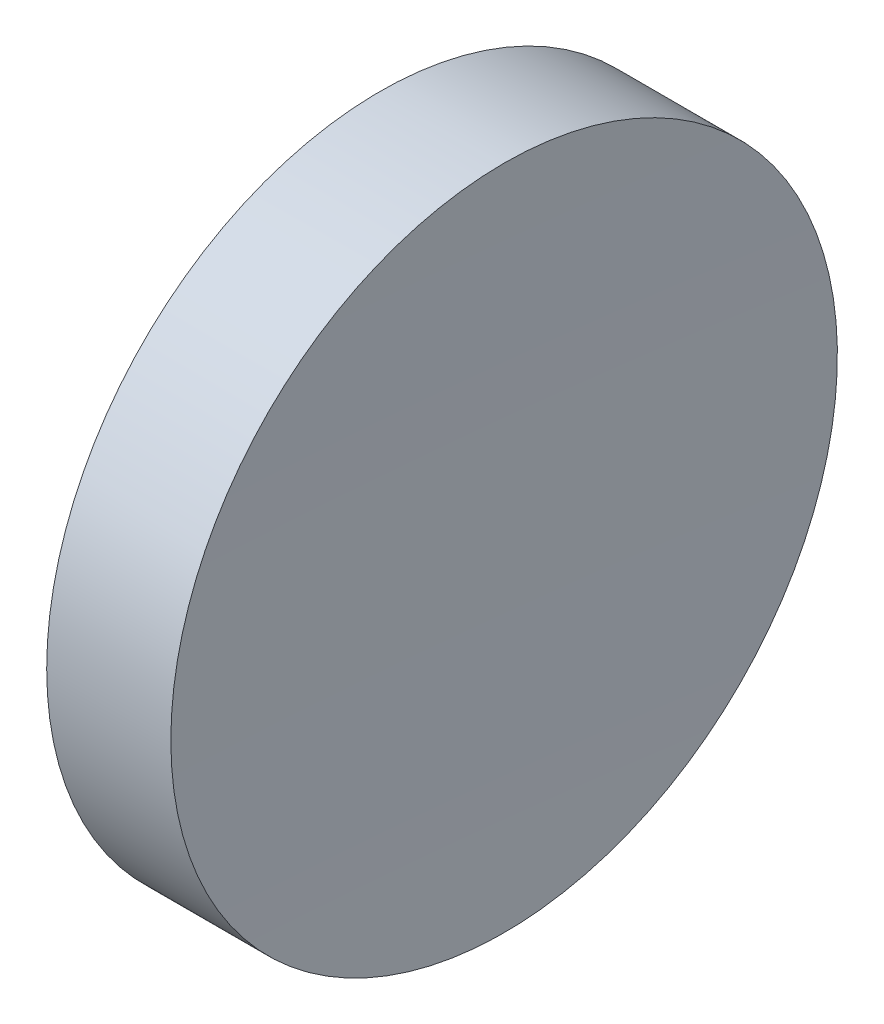
SolidWorks part; units mm, degrees
ref_plane "前视基准面" through (0, 0, 0) normal (0, 0, 1) x (1, 0, 0)
ref_plane "上视基准面" through (0, 0, 0) normal (0, 1, 0) x (1, 0, 0)
ref_plane "右视基准面" through (0, 0, 0) normal (1, 0, 0) x (0, 0, -1)
sketch "草图1" plane through (0, 0, 0) normal (0, 0, 1) x (1, 0, 0)
  line L0 (217.9703, 138.756) -> (265.5527, 138.756) construction
  line L1 (230.1853, 138.756) -> (230.1853, 163.756)
  line L2 (239.1853, 138.756) -> (230.1853, 138.756)
  line L3 (230.1853, 163.756) -> (239.4979, 163.756)
  arc A0 (239.4979, 163.756) -> (239.1853, 138.756) centre (1239.1853, 138.756) ccw
  dimension "D1" = 1000
  dimension "D2" = 9.3125
revolve "旋转1" add sketch "草图1" angle 360 about L0
